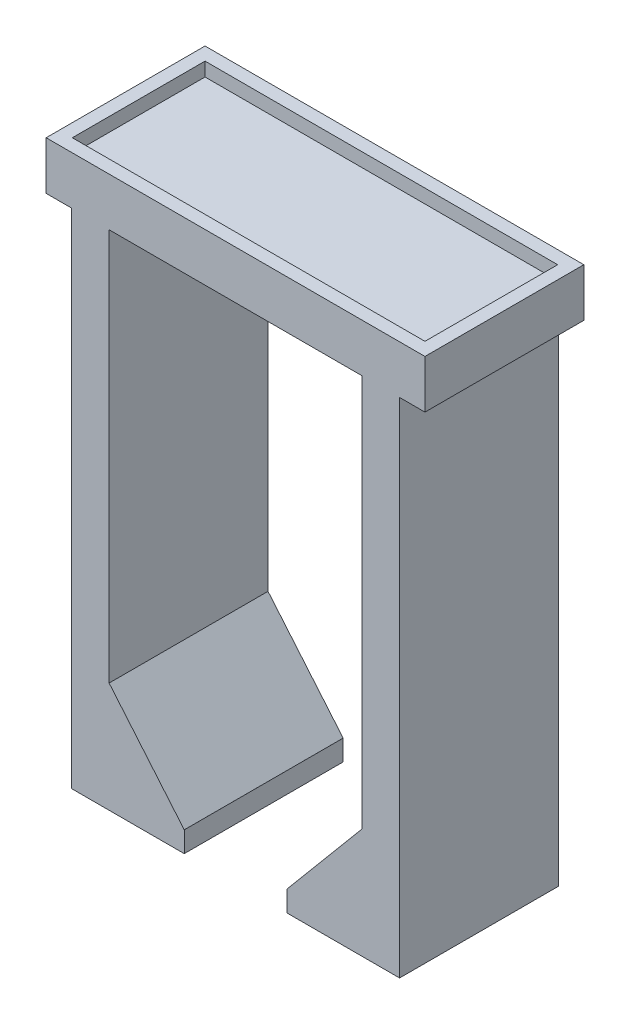
SolidWorks part; units mm, degrees
material "ABS"
ref_plane "Front Plane" through (0, 0, 0) normal (0, 0, 1) x (1, 0, 0)
ref_plane "Top Plane" through (0, 0, 0) normal (0, 1, 0) x (1, 0, 0)
ref_plane "Right Plane" through (0, 0, 0) normal (1, 0, 0) x (0, 0, -1)
sketch "Sketch1" plane through (0, 0, 0) normal (0, 1, 0) x (1, 0, 0)
  line L1 (-3.91, -25.5) -> (3.91, -25.5)
  line L2 (-3.91, -25.5) -> (-3.91, 25.5)
  line L3 (-3.91, 25.5) -> (3.91, 25.5)
  line L4 (3.91, -25.5) -> (3.91, 25.5)
  line L5 (-3.91, -25.5) -> (3.91, 25.5) construction
  line L6 (-3.91, 25.5) -> (3.91, -25.5) construction
  point P0 (0, 0)
extrude "Boss-Extrude1" add sketch "Sketch1" along normal blind 25
sketch "Sketch2" plane through (0, 25, 0) normal (0, 1, 0) x (1, 0, 0)
  line L0 (0, 0) -> (64.6527, 0) construction
  line L1 (0, -9.7005) -> (0, 48.2523) construction
  line L2 (41.0888, 9.535) -> (25.5, 9.535)
  line L3 (25.5, 9.535) -> (25.5, -9.535)
  line L4 (25.5, -9.535) -> (-25.5, -9.535)
  line L5 (-25.5, -9.535) -> (-25.5, 9.535)
  line L6 (-25.5, 9.535) -> (41.0888, 9.535)
  line L7 (-25.5, 9.535) -> (25.5, -9.535) construction
  line L8 (25.5, 9.535) -> (-25.5, -9.535) construction
  line L9 (-27.5, -11.535) -> (27.5, -11.535)
  line L10 (-3.91, -25.5) -> (3.91, -25.5) construction
  line L11 (27.5, -11.535) -> (27.5, 11.535)
  line L12 (27.5, 11.535) -> (-27.5, 11.535)
  line L13 (-27.5, 11.535) -> (-27.5, -11.535)
  point P5 (0, 0)
  point P12 (0, 0)
  dimension "D1" = 25.5
  dimension "D2" = 51
  dimension "D3" = 25.5
  dimension "D4" = 90
  dimension "D5" = 0
  dimension "D7" = 19.07
  dimension "D8" = 2
  dimension "D9" = 2
  dimension "D10" = 2
  dimension "D11" = 2
extrude "Boss-Extrude2" add sketch "Sketch2" along normal blind 5 contours L12 L13 L9 L11
sketch "Sketch3" plane through (0, 30, 0) normal (0, 1, 0) x (1, 0, 0)
  line L0 (-27.5, 11.535) -> (-27.5, -11.535) construction
  line L1 (27.5, 11.535) -> (-27.5, 11.535) construction
  line L2 (27.5, -11.535) -> (27.5, 11.535) construction
  line L4 (27.5, -11.535) -> (27.5, 11.535)
  line L5 (27.5, 11.535) -> (-27.5, 11.535)
  line L6 (-27.5, 11.535) -> (-27.5, -11.535)
  line L7 (-27.5, -11.535) -> (27.5, -11.535)
  line L11 (-27.5, -11.535) -> (27.5, -11.535)
  line L18 (-25.6, 9.635) -> (25.6, 9.635)
  line L19 (25.6, 9.635) -> (25.6, -9.635)
  line L20 (25.6, -9.635) -> (-25.6, -9.635) construction
  line L21 (-25.6, -9.635) -> (-25.6, 9.635)
  line M5 (27.5, -11.535) -> (27.5, 11.535)
  line M6 (27.5, 11.535) -> (-27.5, 11.535)
  line M7 (-27.5, 11.535) -> (-27.5, -11.535)
  line M8 (-27.5, -11.535) -> (27.5, -11.535)
  dimension "D2" = 1.9
  dimension "D3" = 1.9
  dimension "D4" = 1.9
  dimension "D5" = 1.9
  dimension "D1" = 0
extrude "Boss-Extrude3" add sketch "Sketch3" along normal blind 2 contours L20 L21 L18 L19 M8 M5 M6 M7
fillet "Fillet1" radius 10 1 edges at (-3.91, 25, 0)
fillet "Fillet2" radius 3 1 edges at (3.91, 25, 0)
sketch "Sketch4" plane through (-3.91, 0, 0) normal (-1, 0, 0) x (0, 0, 1)
  line L1 (-1.5, -5) -> (1.5, -5)
  line L2 (-1.5, -5) -> (-1.5, 5)
  line L3 (-1.5, 5) -> (1.5, 5)
  line L4 (1.5, -5) -> (1.5, 5)
  line L5 (-1.5, -5) -> (1.5, 5) construction
  line L6 (-1.5, 5) -> (1.5, -5) construction
  line L7 (-25.5, 0) -> (25.5, 0) construction
  point P6 (0, 0)
  point P7 (0, 0)
  dimension "D1" = 0
extrude "Boss-Extrude4" add sketch "Sketch4" along normal blind 2.5
chamfer "Chamfer1" distance 1 angle 45 3 edges at (-3.91, 2.5, -1.5) (-3.91, 5, 0) (-3.91, 2.5, 1.5)
sketch "Sketch5" plane through (0, -5, 0) normal (0, -1, 0) x (-1, 0, 0)
  line L1 (-43.9041, -75.6163) -> (54.3096, -75.6163)
  line L2 (-43.9041, -75.6163) -> (-43.9041, 75.6163)
  line L3 (-43.9041, 75.6163) -> (54.3096, 75.6163)
  line L4 (54.3096, -75.6163) -> (54.3096, 75.6163)
  line L5 (-43.9041, -75.6163) -> (54.3096, 75.6163) construction
  line L6 (-43.9041, 75.6163) -> (54.3096, -75.6163) construction
  point P0 (5.2027, 0)
extrude "Cut-Extrude1" cut sketch "Sketch5" against normal up to vertex (30 mm away) up to point (27.5, 25, -11.535)
ref_plane "Plane1" through (0, 0, 0) normal (1, 0, 0) x (0, 0, -1)
sketch "Sketch6" plane through (0, 25, 0) normal (0, -1, 0) x (-1, 0, 0)
  line L0 (-23.816, 11.535) -> (-18.3582, 11.535)
  line L1 (-27.5, 11.535) -> (27.5, 11.535) construction
  line L2 (-18.3582, 11.535) -> (-18.3582, -11.535)
  line L3 (27.5, -11.535) -> (-27.5, -11.535) construction
  line L4 (-18.3582, -11.535) -> (-23.816, -11.535)
  line L5 (-23.816, -11.535) -> (-23.816, 11.535)
  dimension "D1" = 5.4578
extrude "Boss-Extrude5" add sketch "Sketch6" along normal blind 70
sketch "Sketch7" plane through (0, -45, 0) normal (0, -1, 0) x (-1, 0, 0)
  line L0 (-23.816, 11.535) -> (-7.4475, 11.535)
  line L1 (-7.4475, 11.535) -> (-7.4475, -11.535)
  line L2 (-7.4475, -11.535) -> (-23.816, -11.535)
  line L3 (-23.816, -11.535) -> (-18.3582, -11.535) construction
  line L4 (-23.816, 11.535) -> (-23.816, -11.535)
  line L5 (-23.816, 11.535) -> (-23.816, -11.535) construction
  dimension "D1" = 0
extrude "Boss-Extrude6" add sketch "Sketch7" along normal blind 3
chamfer "Chamfer2" distance 13 angle 40 1 edges at (18.3582, -45, 0)
mirror "Mirror1" about plane through (0, 0, 0) normal (1, 0, 0) of "Chamfer2", "Boss-Extrude6", "Boss-Extrude5"
